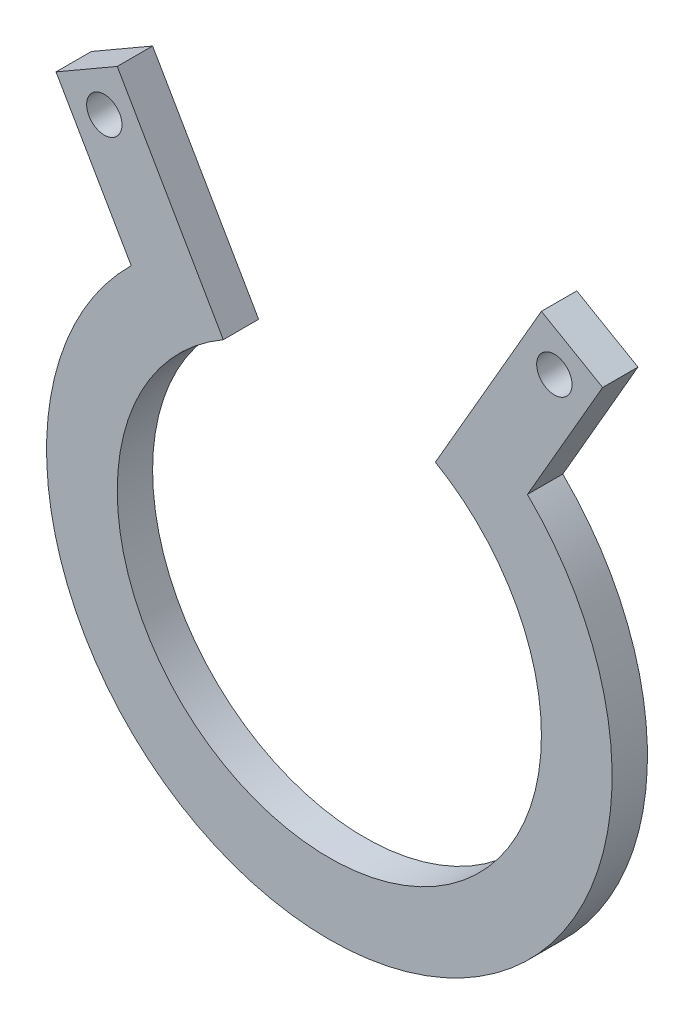
SolidWorks part; units mm, degrees
ref_plane "Front Plane" through (0, 0, 0) normal (0, 0, 1) x (1, 0, 0)
ref_plane "Top Plane" through (0, 0, 0) normal (0, 1, 0) x (1, 0, 0)
ref_plane "Right Plane" through (0, 0, 0) normal (1, 0, 0) x (0, 0, -1)
sketch "Sketch2" plane through (0, 0, 0) normal (0, 0, 1) x (1, 0, 0)
  circle A0 centre (0, 0) radius 22.225
  circle A1 centre (0, 0) radius 25.4
  circle A2 centre (0, 0) radius 19.05
  dimension "D1" = 44.45
  dimension "D2" = 3.175
  dimension "D3" = 3.175
extrude "Boss-Extrude1" add sketch "Sketch2" along normal blind 3.175 contours A1 A0 | A0 A2
sketch "Sketch3" plane through (0, 0, 3.175) normal (0, 0, 1) x (1, 0, 0)
  line L0 (-21.7996, 31.4081) -> (-20.2121, 28.6584) construction
  line L1 (0, 0) -> (-12.7, 21.997) construction
  line L2 (0, 0) -> (0, 25.4) construction
  line L3 (-12.7, 21.997) -> (-19.05, 32.9956)
  line L4 (-19.05, 32.9956) -> (-24.5493, 29.8206)
  line L5 (-24.5493, 29.8206) -> (-17.796, 18.1235)
  line L6 (-19.05, 32.9956) -> (-12.2967, 21.2985)
  line L7 (-18.1993, 18.822) -> (-24.5493, 29.8206)
  line L8 (21.7996, 31.4081) -> (20.2121, 28.6584) construction
  line L9 (18.1993, 18.822) -> (24.5493, 29.8206)
  line L10 (19.05, 32.9956) -> (12.2967, 21.2985)
  line L11 (24.5493, 29.8206) -> (17.796, 18.1235)
  line L12 (19.05, 32.9956) -> (24.5493, 29.8206)
  line L13 (12.7, 21.997) -> (19.05, 32.9956)
  circle A0 centre (0, 0) radius 25.4 construction
  circle A2 centre (-20.2121, 28.6584) radius 1.5875
  circle A3 centre (20.2121, 28.6584) radius 1.5875
  circle M7 centre (0, 0) radius 25.4
  dimension "D5" = 3.175
  dimension "D1" = 30
  dimension "D2" = 3.175
  dimension "D3" = 12.7
  dimension "D4" = 6.35
extrude "Boss-Extrude2" add sketch "Sketch3" against normal up to surface (3.175 mm away) contours L4 L5 L3 A2 M7 | L12 L10 L11 L9 A3 M7 up to face at (25.4, 0, 0)
ref_plane "Plane4" through (-19.05, 32.9956, 3.175) normal (0, 0, 1) x (1, 0, 0)
sketch "Sketch5" plane through (0, 0, 3.175) normal (0, 0, 1) x (1, 0, 0)
  line L0 (-12.7, 21.997) -> (0, 0)
  line L1 (0, 0) -> (12.7, 21.997)
  arc A0 (12.7, 21.997) -> (-12.7, 21.997) centre (0, 0) ccw construction
  arc A1 (12.7, 21.997) -> (-12.7, 21.997) centre (0, 0) ccw
extrude "Cut-Extrude1" cut sketch "Sketch5" against normal up to surface (3.175 mm away) up to face at (0, 20.7191, 0)
